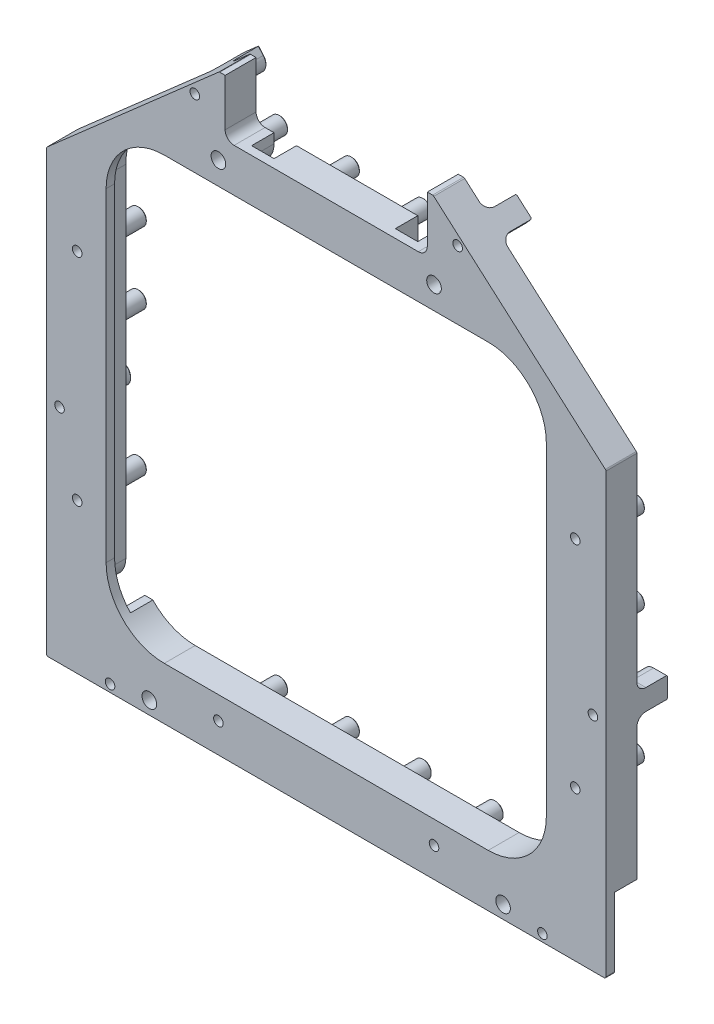
SolidWorks part; units mm, degrees
ref_plane "Front Plane" through (0, 0, 0) normal (0, 0, 1) x (1, 0, 0)
ref_plane "Top Plane" through (0, 0, 0) normal (0, 1, 0) x (1, 0, 0)
ref_plane "Right Plane" through (0, 0, 0) normal (1, 0, 0) x (0, 0, -1)
sketch "Sketch1" plane through (0, 0, 0) normal (0, 0, 1) x (1, 0, 0)
  line L18 (-23.4188, -143.593) -> (-23.4188, -145.6885)
  line L19 (3.25, 2.25) -> (17.07, -2.25) construction
  line L20 (-17.5387, -145.6885) -> (-17.5387, -143.593)
  line L21 (98.8187, -143.593) -> (98.8187, -145.6885)
  line L22 (17.07, -2.25) -> (23.57, 2.25) construction
  line L23 (104.6988, -145.6885) -> (104.6988, -143.593)
  line L24 (116.0431, -85.8906) -> (119.7292, -85.8906)
  line L25 (98.8187, -145.6885) -> (104.6988, -145.6885)
  line L26 (119.7292, -80.0105) -> (116.0431, -80.0105)
  line L27 (80.0077, 10.9154) -> (81.3902, 12.4901)
  line L28 (23.57, 2.25) -> (37.39, -2.25) construction
  line L29 (76.9714, 16.3695) -> (75.5889, 14.7948)
  line L30 (5.6911, 14.7948) -> (4.3085, 16.3695)
  line L31 (37.39, -2.25) -> (43.89, 2.25) construction
  line L32 (-0.1102, 12.4901) -> (1.2723, 10.9154)
  line L33 (-34.7631, -80.0105) -> (-38.4493, -80.0105)
  line L34 (43.89, 2.25) -> (57.71, -2.25) construction
  line L35 (-38.4493, -85.8906) -> (-34.7631, -85.8906)
  line L36 (57.71, -2.25) -> (64.21, 2.25) construction
  line L37 (64.21, 2.25) -> (78.03, -2.25) construction
  line L38 (-27.5156, -35.4005) -> (-32.0156, -49.2205) construction
  line L39 (-32.0156, -49.2205) -> (-27.5156, -55.7205) construction
  line L40 (-27.5156, -55.7205) -> (-32.0156, -69.5405) construction
  line L41 (-32.0156, -69.5405) -> (-27.5156, -76.0405) construction
  line L48 (81.3902, 12.4901) -> (76.9714, 16.3695)
  line L49 (-27.5156, -76.0405) -> (-32.0156, -89.8605) construction
  line L50 (4.3085, 16.3695) -> (-0.1102, 12.4901)
  line L51 (-38.4493, -80.0105) -> (-38.4493, -85.8906)
  line L52 (-23.4188, -145.6885) -> (-17.5387, -145.6885)
  line L53 (119.7292, -85.8906) -> (119.7292, -80.0105)
  line L54 (-32.0156, -89.8605) -> (-27.5156, -96.3605) construction
  line L55 (-27.5156, -96.3605) -> (-32.0156, -110.1805) construction
  line L56 (-32.0156, -110.1805) -> (-27.5156, -116.6805) construction
  line L57 (3.25, -135.0761) -> (17.07, -139.5761) construction
  line L58 (17.07, -139.5761) -> (23.57, -135.0761) construction
  line L59 (23.57, -135.0761) -> (37.39, -139.5761) construction
  line L60 (37.39, -139.5761) -> (43.89, -135.0761) construction
  line L61 (43.89, -135.0761) -> (57.71, -139.5761) construction
  line L62 (57.71, -139.5761) -> (64.21, -135.0761) construction
  line L63 (64.21, -135.0761) -> (78.03, -139.5761) construction
  line L64 (113.2956, -116.6805) -> (108.7956, -110.1805) construction
  line L65 (108.7956, -110.1805) -> (113.2956, -96.3605) construction
  line L66 (113.2956, -96.3605) -> (108.7956, -89.8605) construction
  line L67 (108.7956, -89.8605) -> (113.2956, -76.0405) construction
  line L68 (113.2956, -76.0405) -> (108.7956, -55.7205) construction
  line L69 (108.7956, -55.7205) -> (113.2956, -49.2205) construction
  line L70 (113.2956, -49.2205) -> (108.7956, -35.4005) construction
  line L91 (56.515, 21.6975) -> (56.515, 8.9975) construction
  line L93 (53.34, 5.8225) -> (27.94, 5.8225) construction
  line L95 (24.765, 8.9975) -> (24.765, 21.6975) construction
  line L97 (24.765, 21.6975) -> (10.5686, 21.6975) construction
  line L99 (70.7114, 21.6975) -> (56.515, 21.6975) construction
  arc A6 (-17.5387, -143.593) -> (-23.4188, -143.593) centre (-20.4788, -143.593) ccw
  arc A7 (104.6988, -143.593) -> (98.8187, -143.593) centre (101.7587, -143.593) ccw
  arc A8 (116.0431, -80.0105) -> (116.0431, -85.8906) centre (116.0431, -82.9505) ccw
  arc A9 (75.5889, 14.7948) -> (80.0077, 10.9154) centre (77.7983, 12.8551) ccw
  arc A10 (1.2723, 10.9154) -> (5.6911, 14.7948) centre (3.4817, 12.8551) ccw
  arc A11 (-34.7631, -85.8906) -> (-34.7631, -80.0105) centre (-34.7631, -82.9505) ccw
  circle A22 centre (10.16, 0) radius 2.3813
  circle A23 centre (30.48, 0) radius 2.3812
  circle A25 centre (50.8, 0) radius 2.3812
  circle A27 centre (71.12, 0) radius 2.3813
  circle A29 centre (111.0456, -42.3105) radius 2.3813
  circle A31 centre (111.0456, -65.8805) radius 2.3813
  circle A33 centre (111.0456, -103.2705) radius 2.3813
  circle A35 centre (71.12, -137.3261) radius 2.3813
  circle A36 centre (50.8, -137.3261) radius 2.3812
  circle A37 centre (30.48, -137.3261) radius 2.3812
  circle A38 centre (10.16, -137.3261) radius 2.3813
  circle A39 centre (-29.7656, -103.2705) radius 2.3813
  circle A40 centre (-29.7656, -62.6305) radius 2.3813
  circle A41 centre (-29.7656, -42.3105) radius 2.3813
  arc A53 (53.34, 5.8225) -> (56.515, 8.9975) centre (53.34, 8.9975) ccw construction
  arc A55 (24.765, 8.9975) -> (27.94, 5.8225) centre (27.94, 8.9975) ccw construction
  dimension "D2" = 4.7625
extrude "Boss-Extrude1" add sketch "Sketch1" along normal up to surface (8.6623 mm away)
sketch "Sketch3" plane through (0, 0, 0) normal (0, 0, -1) x (-1, 0, 0)
  line L19 (-71.0466, 21.5712) -> (-119.5564, -21.0176)
  line L20 (-56.515, 8.9975) -> (-56.515, 21.6975)
  line L21 (38.2764, -21.0176) -> (-10.2334, 21.5712)
  line L22 (38.4493, -145.1805) -> (38.4493, -21.3993)
  line L23 (-119.2212, -145.6885) -> (37.9413, -145.6885)
  line L24 (-119.7292, -21.3993) -> (-119.7292, -145.1805)
  line L27 (-102.87, -22.8742) -> (-102.87, -114.4519)
  line L28 (-86.4288, -130.893) -> (5.1489, -130.893)
  line L29 (21.59, -114.4519) -> (21.59, -22.8742)
  line L30 (5.1489, -6.433) -> (-86.4288, -6.433)
  line L51 (-27.94, 5.8225) -> (-53.34, 5.8225)
  line L53 (-24.765, 21.6975) -> (-24.765, 8.9975)
  line L55 (-10.5686, 21.6975) -> (-24.765, 21.6975)
  line L57 (-56.515, 21.6975) -> (-70.7114, 21.6975)
  arc A9 (-102.87, -114.4519) -> (-86.4288, -130.893) centre (-86.4288, -114.4519) ccw
  arc A10 (5.1489, -130.893) -> (21.59, -114.4519) centre (5.1489, -114.4519) ccw
  arc A11 (21.59, -22.8742) -> (5.1489, -6.433) centre (5.1489, -22.8742) ccw
  arc A12 (-86.4288, -6.433) -> (-102.87, -22.8742) centre (-86.4288, -22.8742) ccw
  arc A29 (-70.7114, 21.6975) -> (-71.0466, 21.5712) centre (-70.7114, 21.1895) ccw
  arc A31 (-10.2334, 21.5712) -> (-10.5686, 21.6975) centre (-10.5686, 21.1895) ccw
  arc A37 (38.4493, -21.3993) -> (38.2764, -21.0176) centre (37.9413, -21.3993) ccw
  arc A39 (37.9413, -145.6885) -> (38.4493, -145.1805) centre (37.9413, -145.1805) ccw
  arc A41 (-119.7292, -145.1805) -> (-119.2212, -145.6885) centre (-119.2212, -145.1805) ccw
  arc A43 (-119.5564, -21.0176) -> (-119.7292, -21.3993) centre (-119.2212, -21.3993) ccw
  arc A45 (-56.515, 8.9975) -> (-53.34, 5.8225) centre (-53.34, 8.9975) ccw
  arc A47 (-27.94, 5.8225) -> (-24.765, 8.9975) centre (-27.94, 8.9975) ccw
extrude "Boss-Extrude2" add sketch "Sketch3" against normal up to surface (8.745 mm away) from offset 17.4073
sketch "Sketch6" plane through (0, 0, 8.6623) normal (0, 0, -1) x (-1, 0, 0)
  line L0 (-40.64, 23.2977) -> (-40.64, -6.433) construction
  line L2 (5.1489, -6.433) -> (-86.4288, -6.433) construction
  line L3 (-24.765, 21.6975) -> (-24.765, 8.9975) construction
  line L4 (-12.065, 5.8225) -> (-69.215, 5.8225)
  line L5 (-12.065, 5.8225) -> (-12.065, 21.6975)
  line L6 (-12.065, 21.6975) -> (-69.215, 21.6975)
  line L7 (-69.215, 5.8225) -> (-69.215, 21.6975)
  line L8 (-12.065, 5.8225) -> (-69.215, 21.6975) construction
  line L9 (-12.065, 21.6975) -> (-69.215, 5.8225) construction
  line L10 (-56.515, 8.9975) -> (-56.515, 21.6975) construction
  line L11 (-10.5686, 21.6975) -> (-24.765, 21.6975) construction
  point P6 (-40.64, 13.76)
  dimension "D1" = 57.15
  dimension "D2" = 15.875
  dimension "D3" = 1.6002
extrude "Cut-Extrude1" cut sketch "Sketch6" against normal through all
fillet "Fillet1" radius 2.54 2 edges at (69.215, 5.8225, 13.0348) (12.065, 5.8225, 13.0348)
hole_wizard "Hole1" positions "Sketch8" profile "Sketch7" legacy
sketch "Sketch8" plane through (0, 0, 17.4073) normal (0, 0, 1) x (1, 0, 0)
  line L3 (40.64, 24.3645) -> (40.64, -145.6885) construction
  line L7 (-17.5387, -145.6885) -> (98.8187, -145.6885) construction
  point P0 (10.16, 0)
  point P3 (-9.3663, -142.0055)
  point P26 (71.12, 0)
  point P27 (90.6462, -142.0055)
sketch "Sketch7" plane through (10.16, 0, 17.4073) normal (1, 0, 0) x (0, -1, 0)
  line L0 (0, 0) -> (0, 3.429)
  line L1 (0, 3.429) -> (1.9431, 3.429)
  line L2 (1.9431, 3.429) -> (2.0701, 0)
  line L3 (2.0701, 0) -> (0, 0)
  line L4 (0, 110) -> (0, -10) construction
  dimension "Minor Diameter" = 3.8862
  dimension "Depth" = 3.429
  dimension "Major Diameter" = 4.1402
hole_wizard "#4 Clearance Hole1" positions "Sketch10" profile "Sketch11" hole size "#4" standard "ANSI Inch" end condition through all
sketch "Sketch10" plane through (0, 0, 17.4073) normal (0, 0, 1) x (1, 0, 0)
  point P0 (10.16, 0)
  point P3 (71.12, 0)
  point P6 (-9.3663, -142.0055)
  point P9 (90.6462, -142.0055)
sketch "Sketch11" plane through (10.16, 0, 17.4073) normal (1, 0, 0) x (0, -1, 0)
  line L0 (0, 0) -> (0, 17.4073)
  line L1 (0, 17.4073) -> (1.7272, 17.4073)
  line L2 (1.7272, 17.4073) -> (1.7272, 0)
  line L5 (1.7272, 0) -> (0, 0)
  line L11 (0, -6.35) -> (0, 107.95) construction
  dimension "Thru Hole Dia." = 3.4544
  dimension "Thru Hole Depth" = 17.4073
hole_wizard "Hole2" positions "Sketch15" profile "Sketch14" legacy
sketch "Sketch15" plane through (0, 0, 0) normal (0, 0, -1) x (-1, 0, 0)
  point P0 (-77.7983, 12.8551)
  point P3 (-3.4817, 12.8551)
  point P6 (-116.0431, -82.9505)
  point P9 (34.7631, -82.9505)
  point P12 (20.4788, -143.593)
  point P15 (-101.7587, -143.593)
  point P18 (-71.12, 0)
  point P21 (-10.16, 0)
  point P24 (29.7656, -42.3105)
  point P27 (-111.0456, -42.3105)
  point P30 (-111.0456, -103.2705)
  point P33 (29.7656, -103.2705)
  point P36 (-10.16, -137.3261)
  point P39 (-71.12, -137.3261)
sketch "Sketch14" plane through (77.7983, 12.8551, 0) normal (1, 0, 0) x (0, 1, 0)
  line L0 (0, 0) -> (0, 2.921)
  line L1 (0, 2.921) -> (1.4986, 2.921)
  line L2 (1.4986, 2.921) -> (1.6383, 0)
  line L3 (1.6383, 0) -> (0, 0)
  line L4 (0, 110) -> (0, -10) construction
  dimension "Minor Diameter" = 2.9972
  dimension "Depth" = 2.921
  dimension "Major Diameter" = 3.2766
hole_wizard "#2 Clearance Hole1" positions "Sketch17" profile "Sketch16" hole size "#2" standard "ANSI Inch" end condition through all
sketch "Sketch17" plane through (0, 0, 0) normal (0, 0, -1) x (-1, 0, 0)
  point P0 (-101.7587, -143.593)
  point P3 (20.4788, -143.593)
  point P6 (34.7631, -82.9505)
  point P9 (-116.0431, -82.9505)
  point P12 (-77.7983, 12.8551)
  point P15 (-3.4817, 12.8551)
  point P18 (-111.0456, -42.3105)
  point P21 (29.7656, -42.3105)
  point P24 (29.7656, -103.2705)
  point P27 (-10.16, -137.3261)
  point P30 (-71.12, -137.3261)
  point P34 (-111.0456, -103.2705)
  point P37 (-71.12, 0)
  point P40 (-10.16, 0)
sketch "Sketch16" plane through (101.7587, -143.593, 0) normal (1, 0, 0) x (0, 1, 0)
  line L0 (0, 0) -> (0, 17.4073)
  line L1 (0, 17.4073) -> (1.3525, 17.4073)
  line L2 (1.3525, 17.4073) -> (1.3525, 0)
  line L5 (1.3525, 0) -> (0, 0)
  line L11 (0, -6.35) -> (0, 107.95) construction
  dimension "Thru Hole Dia." = 2.7051
  dimension "Thru Hole Depth" = 17.4073
fillet "Fillet2" radius 2.54 32 edges at (-20.4788, -140.653, 8.6623) (-36.6062, -80.0105, 8.6623) (-31.823, -82.9505, 8.6623) (0.581, 11.7027, 8.6623) (4.9998, 15.5822, 8.6623) (76.2802, 15.5822, 8.6623) (80.6989, 11.7027, 8.6623) (117.8861, -80.0105, 8.6623) (117.8861, -85.8906, 8.6623) (104.6988, -144.6408, 8.6623) (101.7587, -140.653, 8.6623) (-29.7656, -105.6518, 8.6623) (-36.6062, -85.8906, 8.6623) (-29.7656, -65.0118, 8.6623) (-29.7656, -44.6918, 8.6623) (5.4214, 10.6457, 8.6623) (10.16, -2.3812, 8.6623) (30.48, -2.3812, 8.6623) (50.8, -2.3812, 8.6623) (71.12, -2.3812, 8.6623) (75.8586, 10.6457, 8.6623) (111.0456, -44.6918, 8.6623) (111.0456, -68.2618, 8.6623) (113.103, -82.9505, 8.6623) (111.0456, -105.6518, 8.6623) (98.8187, -144.6408, 8.6623) (71.12, -139.7073, 8.6623) (50.8, -139.7073, 8.6623) (30.48, -139.7073, 8.6623) (10.16, -139.7073, 8.6623)
chamfer "Chamfer1" distance 0.254 angle 45 38 edges at (-27.3844, -42.3105, 0) (-27.3844, -62.6305, 0) (-27.3844, -103.2705, 0) (12.5412, -137.3261, 0) (32.8612, -137.3261, 0) (53.1812, -137.3261, 0) (73.5012, -137.3261, 0) (113.4269, -103.2705, 0) (113.4269, -65.8805, 0) (113.4269, -42.3105, 0) (117.8861, -80.0105, 0) (113.103, -82.9505, 0) (117.8861, -85.8906, 0) (104.6988, -144.6408, 0) (98.8187, -144.6408, 0) (101.7587, -140.653, 0) (-17.5387, -144.6408, 0) (-23.4188, -144.6408, 0) (-20.4788, -140.653, 0) (-36.6062, -85.8906, 0) (-36.6062, -80.0105, 0) (-31.823, -82.9505, 0) (76.2802, 15.5822, 0) (80.6989, 11.7027, 0) (75.8586, 10.6457, 0) (73.5012, 0, 0) (53.1812, 0, 0) (32.8612, 0, 0) (4.9998, 15.5822, 0) (5.4214, 10.6457, 0) (0.581, 11.7027, 0) (12.5412, 0, 0) (-31.4039, -42.3105, 0) (-31.4039, -103.2705, 0) (8.5217, -137.3261, 0) (69.4817, -137.3261, 0) (109.4073, -103.2705, 0) (109.4073, -42.3105, 0)
sketch "Sketch18" plane through (0, 0, 8.6623) normal (0, 0, -1) x (-1, 0, 0)
  line L1 (-107.2388, -145.6885) -> (-119.2212, -145.6885) construction
  line L2 (-119.7292, -145.1805) -> (-119.7292, -125.7241)
  line L3 (-119.7292, -125.7241) -> (-100.6792, -125.7241)
  line L4 (-100.6792, -138.2204) -> (-100.6792, -125.7241)
  line L5 (-119.7292, -145.1805) -> (-100.6792, -125.7241) construction
  line L6 (-119.7292, -125.7241) -> (-102.11, -138.1243) construction
  line L7 (-107.2388, -145.6885) -> (-107.2388, -143.593) construction
  line L8 (-107.2388, -145.6885) -> (-107.2388, -143.593)
  line L9 (-107.2388, -145.6885) -> (-119.2212, -145.6885)
  arc A0 (-96.2787, -143.593) -> (-107.2388, -143.593) centre (-101.7587, -143.593) ccw construction
  arc A1 (-100.6792, -138.2204) -> (-107.2388, -143.593) centre (-101.7587, -143.593) ccw
  arc A2 (-119.7292, -145.1805) -> (-119.2212, -145.6885) centre (-119.2212, -145.1805) ccw construction
  arc A3 (-119.7292, -145.1805) -> (-119.2212, -145.6885) centre (-119.2212, -145.1805) ccw
  point P4 (-108.4509, -133.6616)
  point P12 (-111.0456, -133.6616)
  point P13 (-111.0456, -133.6616)
  dimension "D1" = 7.9375
  dimension "D2" = 19.05
extrude "Cut-Extrude2" cut sketch "Sketch18" against normal blind 6.35
sketch "Sketch19" plane through (0, 0, 8.6623) normal (0, 0, -1) x (-1, 0, 0)
  line L0 (-86.4288, -6.433) -> (5.1489, -6.433) construction
  line L1 (-102.87, -114.4519) -> (-102.87, -22.8742) construction
  line L2 (-86.4288, -6.433) -> (-57.785, -6.433)
  line L3 (-102.87, -114.4519) -> (-102.87, -22.8742)
  line L4 (-106.045, -114.4519) -> (-106.045, -22.8742)
  line L5 (-86.4288, -3.258) -> (-64.135, -3.258)
  line L6 (-60.96, -3.258) -> (-60.96, 5.8225) construction
  line L7 (-66.675, 5.8225) -> (-14.605, 5.8225) construction
  line L8 (-66.1987, 0) -> (-55.7212, 0) construction
  line L9 (-57.785, -3.258) -> (-57.785, 5.8225)
  line L10 (-64.135, -3.258) -> (-64.135, 5.8225)
  line L11 (-57.785, -3.258) -> (-57.785, -6.433)
  line L12 (-86.4288, -3.258) -> (5.1489, -3.258) construction
  line L13 (-86.4288, -6.433) -> (5.1489, -6.433) construction
  line L14 (-106.045, -114.4519) -> (-106.045, -125.7241)
  line L15 (-100.6792, -125.7241) -> (-119.7292, -125.7241) construction
  line L16 (-106.045, -125.7241) -> (-98.3975, -125.7241)
  line L17 (-64.135, 5.8225) -> (-57.785, 5.8225)
  arc A0 (-86.4288, -6.433) -> (-102.87, -22.8742) centre (-86.4288, -22.8742) ccw construction
  arc A1 (-102.87, -114.4519) -> (-86.4288, -130.893) centre (-86.4288, -114.4519) ccw construction
  arc A2 (-86.4288, -6.433) -> (-102.87, -22.8742) centre (-86.4288, -22.8742) ccw
  arc A3 (-102.87, -114.4519) -> (-98.3975, -125.7241) centre (-86.4288, -114.4519) ccw
  arc A4 (-86.4288, -3.258) -> (-106.045, -22.8742) centre (-86.4288, -22.8742) ccw
  circle A5 centre (-71.12, 0) radius 4.9213 construction
  circle A6 centre (-50.8, 0) radius 4.9212 construction
  point P23 (-60.96, 0)
  dimension "D2" = 3.175
  dimension "D1" = 3.175
  dimension "D3" = 3.175
extrude "Cut-Extrude3" cut sketch "Sketch19" against normal blind 6.35 and the other way up to next
fillet "Fillet3" radius 6.35 2 edges at (64.135, -3.258, 11.8373) (106.045, -125.7241, 11.8373)
ref_plane "Plane1" through (40.64, 0, 0) normal (1, 0, 0) x (0, 0, -1)
mirror "Mirror1" about plane through (40.64, 0, 0) normal (1, 0, 0) of "Fillet3", "Cut-Extrude3", "Cut-Extrude2"
